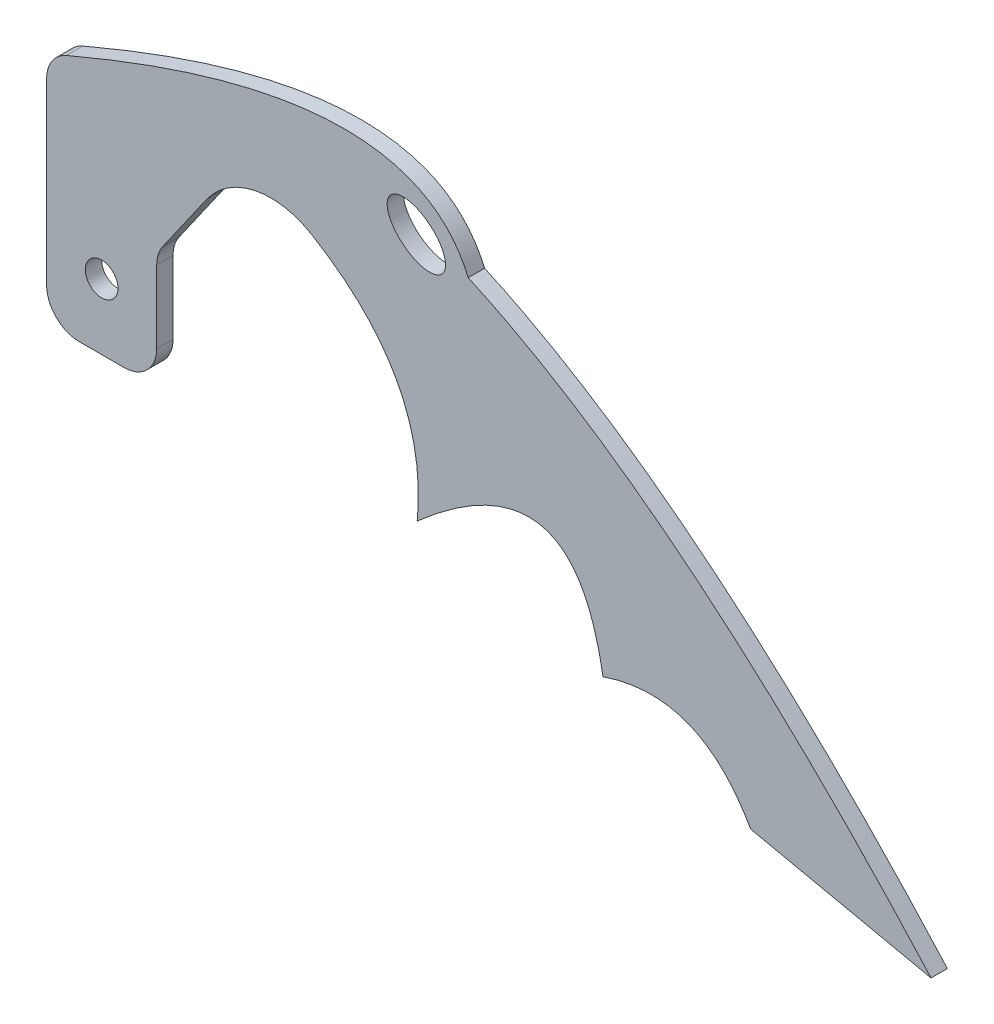
SolidWorks part; units mm, degrees
ref_plane "Front Plane" through (0, 0, 0) normal (0, 0, 1) x (1, 0, 0)
ref_plane "Top Plane" through (0, 0, 0) normal (0, 1, 0) x (1, 0, 0)
ref_plane "Right Plane" through (0, 0, 0) normal (1, 0, 0) x (0, 0, -1)
sketch "Sketch1" plane through (0, 0, 0) normal (0, 0, 1) x (1, 0, 0)
  line L0 (85.838, -35.6868) -> (50.8154, -28.1694)
  line L3 (-47.4408, 35.3674) -> (-64.4615, 11.041)
  line L4 (-64.4615, 11.041) -> (-64.4615, -11.3887)
  line L5 (-64.4615, -11.3887) -> (-85.838, -11.3887)
  line L6 (-85.838, -11.3887) -> (-85.838, 33.807)
  circle A0 centre (-75.1497, 1.3237) radius 3.175
  ellipse E0 centre (-14.0659, 39.3465) end of major axis (-19.1981, 43.3382) minor radius 3.9177
  spline S0 degree 2 poles (85.838, -35.6868) (37.0454, 18.6313) (-3.9965, 37.1134) knots 0 0 0 0.371924 0.371924 0.371924
  spline S1 degree 2 poles (22.1515, -16.8831) (40.9335, -10.4779) (50.8154, -28.1694) knots 0 0 0 1 1 1
  spline S2 degree 2 poles (-47.4408, 35.3674) (-10.9423, 21.5659) (-13.8981, -8.7346) knots 0 0 0 1 1 1
  spline S3 degree 2 poles (-13.8981, -8.7346) (16.3544, 17.8321) (22.1515, -16.8831) knots 0 0 0 1 1 1
  spline S6 degree 2 poles (-85.838, 33.807) (-15.7088, 64.7051) (-3.9965, 37.1134) knots 0 0 0 0.40677 0.40677 0.40677
  dimension "D2" = 6.35
extrude "Boss-Extrude1" add sketch "Sketch1" along normal blind 3.175
fillet "Fillet1" radius 6.35 3 edges at (-64.4615, 11.041, 1.5875) (-85.838, -11.3887, 1.5875) (-64.4615, -11.3887, 1.5875)
fillet "Fillet2" radius 15.24 1 edges at (-47.4408, 35.3674, 1.5875)
fillet "Fillet3" radius 6.35 1 edges at (-85.838, 33.807, 1.5875)
